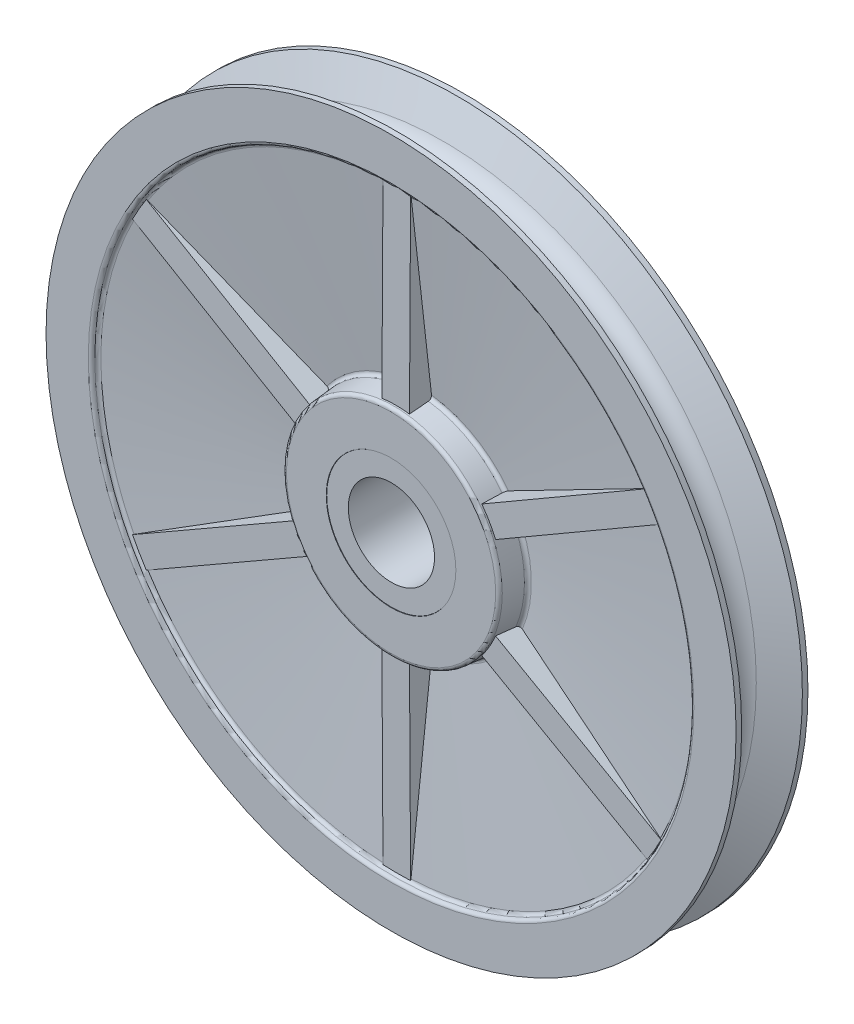
SolidWorks part; units mm, degrees
ref_plane "Front" through (0, 0, 0) normal (0, 0, 1) x (1, 0, 0)
ref_plane "Top" through (0, 0, 0) normal (0, 1, 0) x (1, 0, 0)
ref_plane "Right" through (0, 0, 0) normal (1, 0, 0) x (0, 0, -1)
sketch "Sketch1" plane through (0, 0, 0) normal (1, 0, 0) x (0, 0, -1)
  line L0 (6.7056, 76.2) -> (7.9375, 76.2)
  line L1 (-6.7056, 76.2) -> (-7.9375, 76.2)
  line L2 (-6.7056, 76.2) -> (-3.6467, 69.0776)
  line L3 (7.9375, 23.8125) -> (7.9375, 14.2875)
  line L4 (7.8613, 9.525) -> (-7.8613, 9.525)
  line L5 (-7.9375, 14.2875) -> (-7.9375, 23.8125)
  line L6 (6.7056, 76.2) -> (3.6467, 69.0776)
  line L8 (-7.9375, 0) -> (7.9375, 0) construction
  line L10 (7.9375, 76.2) -> (7.9375, 66.167)
  line L12 (-7.9375, 14.2875) -> (-7.8613, 14.2875)
  line L13 (-7.8613, 14.2875) -> (-7.8613, 9.525)
  line L14 (0, 66.675) -> (0, -66.675) construction
  line L15 (7.8613, 14.2875) -> (7.9375, 14.2875)
  line L16 (7.8613, 14.2875) -> (7.8613, 9.525)
  line L17 (-7.9375, 76.2) -> (-7.9375, -76.2) construction
  line L18 (-7.9375, 66.167) -> (-6.6675, 66.167)
  line L19 (-6.6675, 66.167) -> (-1.905, 23.8125)
  line L20 (-1.905, 23.8125) -> (-7.9375, 23.8125)
  line L21 (-7.9375, 66.167) -> (-7.9375, 76.2)
  line L22 (7.9375, 66.167) -> (6.6675, 66.167)
  line L23 (6.6675, 66.167) -> (1.905, 23.8125)
  line L24 (1.905, 23.8125) -> (7.9375, 23.8125)
  arc A0 (-3.6467, 69.0776) -> (3.6467, 69.0776) centre (0, 70.6437) ccw
  circle A1 centre (0, 70.6437) radius 3.9687 construction
  circle A2 centre (0, 0) radius 9.525 construction
  circle A3 centre (0, 0) radius 14.2875 construction
  circle A4 centre (0, 0) radius 23.8125 construction
  circle A5 centre (0, -70.6437) radius 3.9687 construction
  point P28 (-7.9375, 0)
  dimension "Rope Dia" = 7.9375
  dimension "Shaft Dia" = 19.05
  dimension "D1" = 28.575
  dimension "D3" = 47.625
  dimension "Wd" = 15.875
  dimension "D8" = 1.2319
  dimension "D9" = 0.0762
  dimension "Groove Dia" = 133.35
  dimension "OD" = 152.4
  dimension "D4" = 0.508
  dimension "D2" = 1.27
  dimension "D5" = 3.81
revolve "Revolve1" add sketch "Sketch1" angle 360 about L8
sketch "Sketch2" plane through (0, 0, 0) normal (0, 0, 1) x (1, 0, 0)
  circle A0 centre (0, 0) radius 14.2875 construction
  circle A1 centre (0, 0) radius 14.2875
extrude "Cut-Extrude-Thin1" cut sketch "Sketch2" against normal through all and the other way through all thin
draft "Draft1" type of draft neutral plane draft angle 5 faces to draft 2 face at (23.8125, 0, 7.9375) face at (66.167, 0, 6.6675) neutral plane through (0, 66.167, 7.9375) neutral plane normal (0, 0, 1) parameters "D1"=5
draft "Draft2" type of draft neutral plane draft angle 15 faces to draft 2 face at (23.8125, 0, -1.905) face at (66.167, 0, -7.9375) neutral plane through (0, 76.2, -7.9375) neutral plane normal (0, 0, -1) parameters "D1"=15
fillet "Fillet1" radius 0.762 4 edges at (66.167, 0, 7.9375) (66.167, 0, -7.9375) (23.8125, 0, 7.9375) (23.8125, 0, -7.9375)
fillet "Fillet2" radius 0.762 2 edges at (-24.3351, 0, 1.9638) (66.0548, 0, 6.6549)
sketch "Sketch5" plane through (0, 0, 0) normal (1, 0, 0) x (0, 0, -1)
  line L0 (-6.9215, 22.5425) -> (-6.6675, 66.167)
  line L1 (0, 66.675) -> (0, -66.675) construction
  line L6 (-6.6675, 66.167) -> (0, 66.167)
  line L7 (0, 66.167) -> (0, 14.2875)
  line L11 (-6.9215, 22.5425) -> (-6.9215, 14.2875)
  line L12 (-6.9215, 14.2875) -> (0, 14.2875)
  line L13 (-1.905, 23.8125) -> (-7.9375, 23.8125) construction
  line L14 (-7.9375, 14.2875) -> (-7.9375, 23.8125) construction
  dimension "D1" = 1.27
  dimension "D2" = 1.016
extrude "Boss-Extrude1" add sketch "Sketch5" along normal mid plane 6.096
mirror "Mirror1" about plane through (0, 0, 0) normal (0, 0, 1) of "Boss-Extrude1"
pattern_circular "CirPattern1" count 6 over 360 about axis through (0, 0, 0) along (0, 0, 1) of "Mirror1", "Boss-Extrude1"
equation "\"D1@Sketch1\" = \"Shaft Dia@Sketch1\" * 1.5"
equation "\"D3@Sketch1\" = \"Shaft Dia@Sketch1\" * 2.5"
equation "\"D1@Boss-Extrude1\" = \"OD@Sketch1\" * .04"
